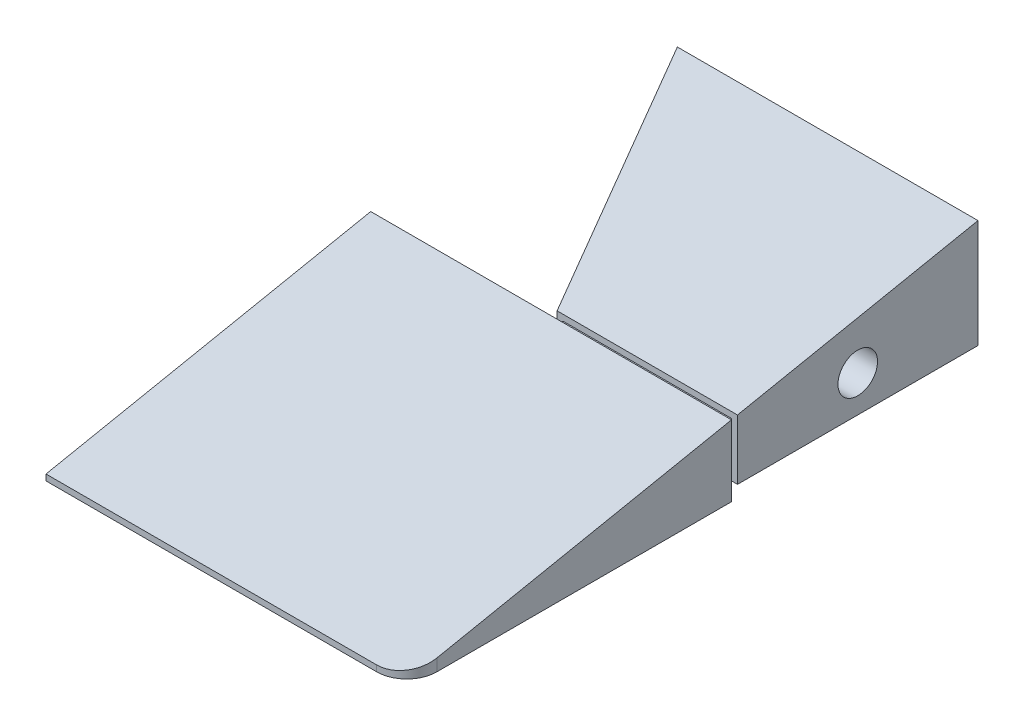
SolidWorks part; units mm, degrees
material "AISI 1020"
ref_plane "Plano frontal" through (0, 0, 0) normal (0, 0, 1) x (1, 0, 0)
ref_plane "Plano superior" through (0, 0, 0) normal (0, 1, 0) x (1, 0, 0)
ref_plane "Plano direito" through (0, 0, 0) normal (1, 0, 0) x (0, 0, -1)
sketch "Esboço1" plane through (0, 0, 0) normal (0, 0, 1) x (1, 0, 0)
  line L1 (-65, 10) -> (65, 10)
  line L2 (-65, 10) -> (-65, -10)
  line L3 (-65, -10) -> (65, -10)
  line L4 (65, 10) -> (65, -10)
  line L5 (-65, 10) -> (65, -10) construction
  line L6 (-65, -10) -> (65, 10) construction
  point P0 (0, 0)
  dimension "D1" = 130
  dimension "D2" = 20
extrude "Ressalto-extrusão1" add sketch "Esboço1" along normal blind 95
sketch "Esboço2" plane through (0, 10, 0) normal (0, 1, 0) x (1, 0, 0)
  line L0 (15, 0) -> (-65, 0)
  line L2 (65, -95) -> (65, 0) construction
  line L3 (35, -40) -> (15, 0)
  line L4 (-65, -95) -> (-65, 0) construction
  line L6 (-65, -95) -> (-65, 0)
  line L7 (65, -95) -> (-65, -95) construction
  line L8 (65, 0) -> (-65, 0) construction
  line L9 (5, -95) -> (-65, -95)
  line L10 (35, -40) -> (35, -41)
  line L11 (35, -41) -> (5, -41)
  line L12 (5, -41) -> (5, -95)
  dimension "D3" = 70
  dimension "D5" = 1
  dimension "D1" = 50
  dimension "D2" = 30
  dimension "D4" = 40
extrude "Corte-extrusão2" cut sketch "Esboço2" against normal up to next contours L3 L0 L6 L9 L12 L11 L10
sketch "Esboço3" plane through (65, 0, 0) normal (1, 0, 0) x (0, 0, -1)
  line L0 (0, 10) -> (-95, -9)
  line L1 (-95, -10) -> (-95, 10) construction
  dimension "D1" = 1
extrude "Corte-extrusão3" cut sketch "Esboço3" against normal through all and the other way through all flip side to cut
hole_wizard "Broca de rosquear de cano para tarraxa de 1/82" positions "Esboço7" profile "Esboço8" hole size "1/8" standard "Ansi Inch"
sketch "Esboço7" plane through (65, 0, 0) normal (1, 0, 0) x (0, 0, -1)
  line L0 (0, -10) -> (0, 10) construction
  line L1 (-95, -10) -> (0, -10) construction
  point P0 (-20, -1.945)
  dimension "D1" = 20
  dimension "D2" = 8.055
sketch "Esboço8" plane through (65, -1.945, 20) normal (0, 1, 0) x (0, 0, -1)
  line L0 (0, 0) -> (0, 11.9768)
  line L1 (0, 11.9768) -> (3.29, 10)
  line L2 (3.29, 10) -> (3.29, 0)
  line L5 (3.29, 0) -> (0, 0)
  line L10 (0, 11.9768) -> (-3.29, 10) construction
  line L11 (0, -6.35) -> (0, 107.95) construction
  dimension "Hole Dia." = 6.58
  dimension "Hole Depth" = 10
  dimension "Drill Angle" = 118
hole_wizard "Broca de rosquear de cano para tarraxa de 1/83" positions "Esboço10" profile "Esboço11" hole size "1/8" standard "Ansi Inch"
sketch "Esboço10" plane through (12, 0, -6) normal (-0.8944, 0, 0.4472) x (0.4472, 0, 0.8944)
  line L0 (6.7082, -10) -> (6.7082, 10) construction
  line L1 (6.7082, -10) -> (51.4296, -10) construction
  point P0 (26.7082, -1.945)
  dimension "D1" = 20
  dimension "D2" = 8.055
sketch "Esboço11" plane through (23.9443, -1.945, 17.8885) normal (0, 1, 0) x (0.4472, 0, 0.8944)
  line L0 (0, 0) -> (0, 11.9768)
  line L1 (0, 11.9768) -> (3.29, 10)
  line L2 (3.29, 10) -> (3.29, 0)
  line L5 (3.29, 0) -> (0, 0)
  line L10 (0, 11.9768) -> (-3.29, 10) construction
  line L11 (0, -6.35) -> (0, 107.95) construction
  dimension "Hole Dia." = 6.58
  dimension "Hole Depth" = 10
  dimension "Drill Angle" = 118
fillet "Filete2" radius 5 1 edges at (65, -9.5, 95)
sketch "Esboço12" plane through (65, 0, 0) normal (1, 0, 0) x (0, 0, -1)
  line L0 (-41, -10) -> (-41, 1.8)
  line L1 (-41, -10) -> (-41, 1.8) construction
  line L2 (-41, 1.8) -> (-40, 2)
  line L3 (-40, 2) -> (-40, -10)
  line L4 (-40, -10) -> (-40, 2) construction
  line L5 (-90, -10) -> (0, -10) construction
  line L6 (-40, -10) -> (-41, -10)
extrude "Corte-extrusão4" cut sketch "Esboço12" against normal up to next
sketch "Esboço13" plane through (0, 0, 40) normal (0, 0, 1) x (1, 0, 0)
  line L0 (35, 2) -> (65, 2) construction
  line L1 (36, 1) -> (64, 1)
  line L2 (36, 1) -> (36, -7)
  line L3 (36, -7) -> (64, -7)
  line L4 (64, 1) -> (64, -7)
  line L5 (36, 1) -> (64, -7) construction
  line L6 (36, -7) -> (64, 1) construction
  line L7 (65, -10) -> (65, 2) construction
  line L8 (35, -10) -> (35, 2) construction
  line L9 (35, -10) -> (65, -10) construction
  point P0 (50, -3)
  dimension "D1" = 1
  dimension "D2" = 1
  dimension "D3" = 1
  dimension "D4" = 3
extrude "Ressalto-extrusão2" add sketch "Esboço13" along normal up to next
sketch "Esboço14" plane through (0, 0, 0) normal (0, 0, -1) x (-1, 0, 0)
  line L0 (-65, -10) -> (-65, -8)
  line L1 (-65, -8) -> (-15, -8)
  line L2 (-15, -10) -> (-15, 10) construction
  line L3 (-15, -8) -> (-15, -10)
  line L4 (-5, -10) -> (-65, -10) construction
  line L5 (-15, -10) -> (-65, -10)
extrude "Corte-extrusão5" cut sketch "Esboço14" against normal blind 40.5
